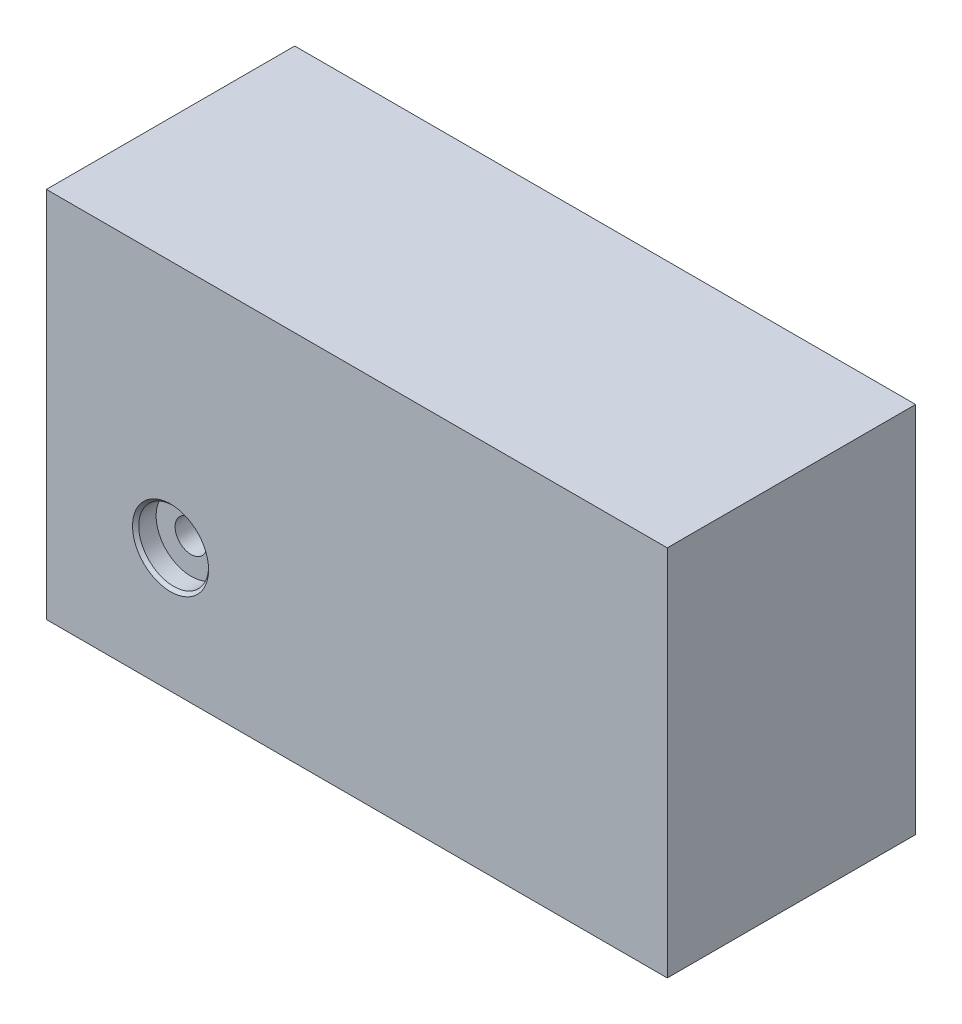
SolidWorks part; units mm, degrees
ref_plane "Front Plane" through (0, 0, 0) normal (0, 0, 1) x (1, 0, 0)
ref_plane "Top Plane" through (0, 0, 0) normal (0, 1, 0) x (1, 0, 0)
ref_plane "Right Plane" through (0, 0, 0) normal (1, 0, 0) x (0, 0, -1)
sketch "Sketch2" plane through (0, 0, 0) normal (0, 0, 1) x (1, 0, 0)
  line L1 (0, 0) -> (127, 0)
  line L2 (0, 0) -> (0, 76.2)
  line L3 (0, 76.2) -> (127, 76.2)
  line L4 (127, 0) -> (127, 76.2)
  dimension "HEIGHT" = 76.2
  dimension "WIDTH" = 127
extrude "Boss-Extrude1" add sketch "Sketch2" along normal blind 50.8
hole_wizard "CBORE for 1/4 Binding Head Machine Screw1" positions "Sketch3" profile "Sketch5" counterbore size "1/4" standard "ANSI Inch" end condition through all
sketch "Sketch3" plane through (0, 0, 50.8) normal (0, 0, 1) x (1, 0, 0)
  line L0 (0, 76.2) -> (0, 0) construction
  line L1 (0, 0) -> (127, 0) construction
  point P0 (25.4, 25.4)
  dimension "D1" = 25.4
  dimension "D2" = 25.4
sketch "Sketch5" plane through (25.4, 25.4, 50.8) normal (1, 0, 0) x (0, -1, 0)
  line L0 (0, 0) -> (0, 50.8)
  line L1 (0, 50.8) -> (3.2639, 50.8)
  line L3 (3.2639, 50.8) -> (3.2639, 4.191)
  line L4 (7.1437, 4.191) -> (3.2639, 4.191)
  line L5 (7.1437, 4.191) -> (7.1437, 0.635)
  line L6 (7.1437, 0.635) -> (7.7788, 0)
  line L7 (7.7788, 0) -> (0, 0)
  line L8 (-7.1437, 0.635) -> (-7.7788, 0) construction
  line L11 (0, -6.35) -> (0, 107.95) construction
  dimension "Thru Hole Dia." = 6.5278
  dimension "Thru Hole Depth" = 50.8
  dimension "C'Bore Dia." = 14.2875
  dimension "C'Bore Depth" = 4.191
  dimension "Near C'Sink Dia." = 15.5575
  dimension "Near C'Sink Angle" = 90
